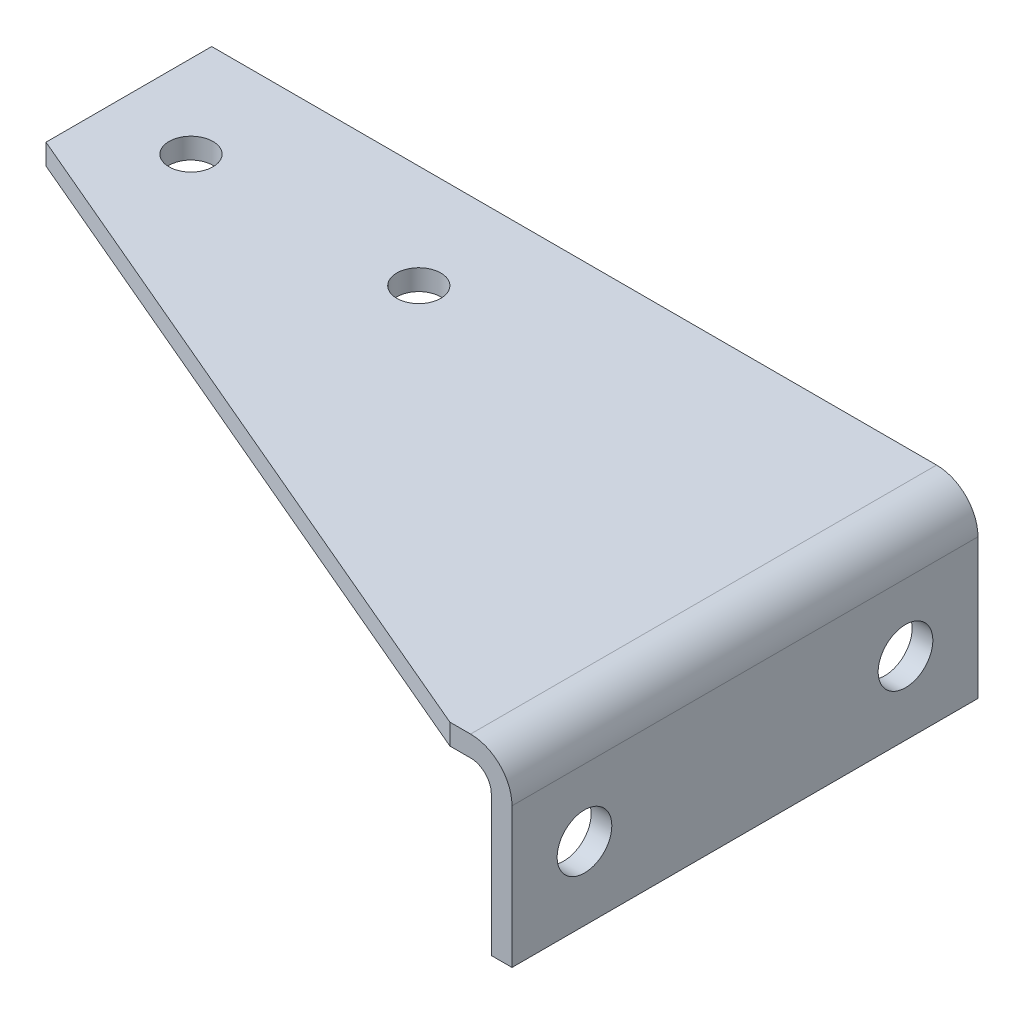
SolidWorks part; units mm, degrees
material "ASTM A36"
ref_plane "Front" through (0, 0, 0) normal (0, 0, 1) x (1, 0, 0)
ref_plane "Top" through (0, 0, 0) normal (0, 1, 0) x (1, 0, 0)
ref_plane "Side" through (0, 0, 0) normal (1, 0, 0) x (0, 0, -1)
sketch "Sketch1" plane through (0, 0, 0) normal (0, 0, 1) x (1, 0, 0)
  line L0 (-228.6, 0) -> (-6.35, 0)
  line L1 (0, -6.35) -> (0, -49.276)
  arc A0 (-6.35, 0) -> (0, -6.35) centre (-6.35, -6.35) cw
  point P6 (0, 0)
  dimension "D3" = 6.35
  dimension "D1" = 228.6
  dimension "D2" = 49.276
extrude "Base-Extrude-Thin" add sketch "Sketch1" along normal blind 142.875 thin thin type one direction reverse wall 6.35
sketch "Sketch2" plane through (0, 0, 0) normal (0, 1, 0) x (1, 0, 0)
  line L0 (-228.6, -50.8) -> (-12.7, -142.875)
  line L1 (-228.6, -142.875) -> (-228.6, 0) construction
  line L2 (6.35, -142.875) -> (6.35, 0) construction
  line L3 (-228.6, 0) -> (-6.35, 0) construction
  line L4 (-228.6, -142.875) -> (-6.35, -142.875) construction
  dimension "D1" = 19.05
  dimension "D2" = 50.8
extrude "Cut cnr" cut sketch "Sketch2" against normal through all and the other way through all flip side to cut
hole_wizard "Hole-flg" positions "Sketch5" profile "Sketch4" legacy end condition through all
sketch "Sketch5" plane through (6.35, 0, 0) normal (1, 0, 0) x (0, 0, -1)
  line L0 (-120.65, -26.924) -> (-22.225, -26.924) construction
  line L3 (-142.875, -6.35) -> (-142.875, -49.276) construction
  line L4 (-142.875, 6.35) -> (0, 6.35) construction
  point P0 (-120.65, -26.924)
  point P1 (-22.225, -26.924)
  dimension "D1" = 33.274
  dimension "D2" = 22.225
  dimension "D3" = 98.425
sketch "Sketch4" plane through (6.35, -26.924, 120.65) normal (0, 1, 0) x (0, 0, -1)
  line L0 (0, 0) -> (0, 234.95)
  line L1 (0, 234.95) -> (8.382, 234.95)
  line L2 (8.382, 234.95) -> (8.382, 0)
  line L3 (8.382, 0) -> (0, 0)
  line L4 (0, 110) -> (0, -10) construction
  dimension "Diameter" = 16.764
  dimension "Depth" = 234.95
hole_wizard "Hole-top" positions "Sketch9" profile "Sketch8" legacy
sketch "Sketch9" plane through (0, 6.35, 0) normal (0, 1, 0) x (-1, 0, 0)
  line L0 (228.6, 0) -> (6.35, 0) construction
  point P0 (203.2, 31.75)
  point P8 (133.35, 31.75)
  dimension "D1" = 69.85
  dimension "D2" = 31.75
  dimension "D3" = 133.35
sketch "Sketch8" plane through (-203.2, 6.35, 31.75) normal (1, 0, 0) x (0, 0, 1)
  line L0 (0, 0) -> (0, 25.4)
  line L1 (0, 25.4) -> (6.7469, 25.4)
  line L2 (6.7469, 25.4) -> (6.7469, 0)
  line L3 (6.7469, 0) -> (0, 0)
  line L4 (0, 110) -> (0, -10) construction
  dimension "Diameter" = 13.4937
  dimension "Depth" = 25.4
mirror "Mirror All1" [suppressed]
sketch "Sketch10" plane through (0, 0, 0) normal (0, 1, 0) x (1, 0, 0)
  line L0 (6.35, -71.4375) -> (-228.6, -25.4)
  line L1 (6.35, -142.875) -> (6.35, 0) construction
  line L2 (-228.6, -50.8) -> (-228.6, 0) construction
extrude "Cut-lh" [suppressed] cut sketch "Sketch10" against normal through all and the other way through all
